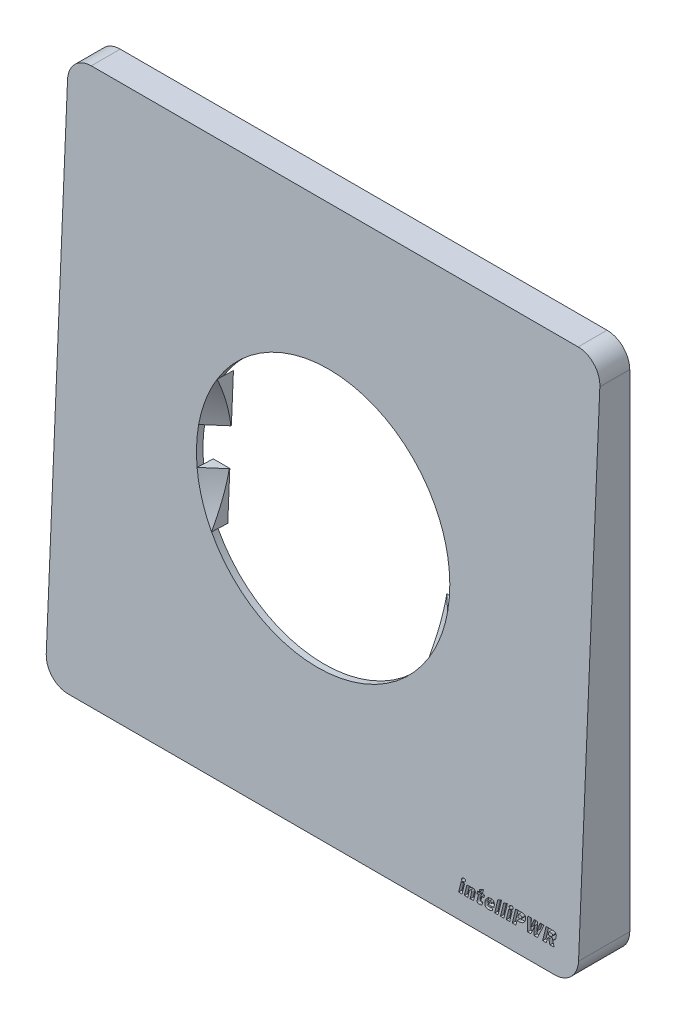
SolidWorks part; units mm, degrees
ref_plane "Front Plane" through (0, 0, 0) normal (0, 0, 1) x (1, 0, 0)
ref_plane "Top Plane" through (0, 0, 0) normal (0, 1, 0) x (1, 0, 0)
ref_plane "Right Plane" through (0, 0, 0) normal (1, 0, 0) x (0, 0, -1)
sketch "Sketch1" plane through (0, 0, 0) normal (0, 0, 1) x (1, 0, 0)
  line L0 (-38.566, 0) -> (72.4153, 0) construction
  line L1 (0, -49.5581) -> (0, 74.5126) construction
  line L2 (-37.5, 40) -> (37.5, 40)
  line L3 (-40, 37.5) -> (-40, -37.5)
  line L4 (-37.5, -40) -> (37.5, -40)
  line L5 (40, 37.5) -> (40, -37.5)
  arc A0 (-40, -37.5) -> (-37.5, -40) centre (-37.5, -37.5) ccw
  arc A1 (37.5, -40) -> (40, -37.5) centre (37.5, -37.5) ccw
  arc A2 (37.5, 40) -> (40, 37.5) centre (37.5, 37.5) cw
  arc A3 (-37.5, 40) -> (-40, 37.5) centre (-37.5, 37.5) ccw
  dimension "D3" = 2.5
  dimension "D1" = 80
  dimension "D2" = 80
  dimension "D4" = 40
  dimension "D5" = 40
extrude "Extrude-Thin1" add sketch "Sketch1" along normal blind 8 thin thin type one direction wall 1
sketch "Sketch5" plane through (41, 0, 0) normal (1, 0, 0) x (0, 0, -1)
  line L0 (20.3178, 0) -> (-25.0092, 0) construction
  line L1 (0, 43.59) -> (0, -45.2443) construction
  line L2 (-3.4562, 41) -> (-8, 41)
  line L3 (-8, 41) -> (-8, -41)
  line L4 (-8, -41) -> (-7.0437, -41)
  line L6 (-7.0437, -41) -> (-3.4562, 41)
  line L7 (-8, -41) -> (0, -41) construction
  line L11 (-8, 41) -> (0, 41) construction
extrude "Cut-Extrude2" cut sketch "Sketch5" against normal blind 120
sketch "Sketch6" plane through (41, 0, 0) normal (1, 0, 0) x (0, 0, -1)
  line L0 (-7.0437, -41) -> (-3.4562, 41)
  line L1 (-3.4562, 41) -> (-4.4572, 41)
  line L2 (-4.4572, 41) -> (-8.0447, -41)
  line L3 (-8.0447, -41) -> (-7.0437, -41)
  line L4 (-3.4562, 41) -> (-3.4562, 45.0301) construction
  dimension "D1" = 1
  dimension "D2" = 90
extrude "Boss-Extrude1" add sketch "Sketch6" against normal blind 82
sketch "Sketch7" plane through (0, 0, 0) normal (0, 0, -1) x (-1, 0, 0)
  line L0 (0, 0) -> (0, 69.537) construction
  line L1 (71.0569, 0) -> (20.5255, 0) construction
  line L2 (-37.5, 41) -> (37.5, 41)
  line L3 (-37.5, 41) -> (37.5, 41) construction
  line L4 (-41, -37.5) -> (-41, 37.5)
  line L5 (41, -37.5) -> (41, 37.5)
  line L6 (-41, -37.5) -> (-41, 37.5) construction
  line L7 (-37.5, -41) -> (37.5, -41)
  arc A0 (37.5, 41) -> (41, 37.5) centre (37.5, 37.5) cw
  arc A1 (-37.5, -41) -> (-41, -37.5) centre (-37.5, -37.5) cw
  arc A2 (37.5, -41) -> (41, -37.5) centre (37.5, -37.5) ccw
  arc A4 (-37.5, 41) -> (-41, 37.5) centre (-37.5, 37.5) ccw
  point P9 (0, -41)
  point P13 (-41, 0)
  point P14 (0, 41)
  point P25 (41, 0)
extrude "Cut-Extrude-Thin1" cut sketch "Sketch7" against normal blind 82 thin thin type one direction wall 11
sketch "Sketch8" plane through (0, 0.273, 6.239) normal (0, 0.0437, 0.999) x (1, 0, 0)
  line L0 (0, 0) -> (0, 28.9526) construction
  line L1 (23.1598, 0) -> (-27.4609, 0) construction
  circle A0 centre (0, 0) radius 19.5
  dimension "D1" = 39
extrude "Cut-Extrude3" cut sketch "Sketch8" against normal blind 82
sketch "Sketch9" plane through (0, 0.273, 6.239) normal (0, 0.0437, 0.999) x (1, 0, 0)
  line L1 (22.5318, -37.8124) -> (22.8563, -36.2774)
  line L3 (22.8563, -36.2774) -> (23.3824, -36.2774)
  line L4 (23.3824, -36.2774) -> (23.058, -37.8124)
  line L5 (23.058, -37.8124) -> (22.5318, -37.8124)
  line L6 (24.2906, -37.8124) -> (24.4746, -36.9301)
  line L7 (24.121, -36.9242) -> (23.9366, -37.8124)
  line L8 (23.9366, -37.8124) -> (23.4104, -37.8124)
  line L9 (23.4104, -37.8124) -> (23.7348, -36.2694)
  line L10 (23.7348, -36.2694) -> (24.261, -36.2694)
  line L11 (24.261, -36.2694) -> (24.2407, -36.3734)
  line L12 (25.0186, -36.8721) -> (24.8197, -37.8124)
  line L13 (24.8197, -37.8124) -> (24.2906, -37.8124)
  line L14 (25.3946, -37.3472) -> (25.5346, -36.6755)
  line L15 (25.5346, -36.6755) -> (25.3007, -36.6755)
  line L16 (25.3007, -36.6755) -> (25.3887, -36.2694)
  line L17 (25.3887, -36.2694) -> (25.6226, -36.2694)
  line L18 (25.6226, -36.2694) -> (25.7042, -35.8811)
  line L19 (25.7042, -35.8811) -> (26.2596, -35.6738)
  line L20 (26.2596, -35.6738) -> (26.134, -36.2694)
  line L21 (26.134, -36.2694) -> (26.4673, -36.2694)
  line L22 (26.4673, -36.2694) -> (26.3797, -36.6755)
  line L23 (26.3797, -36.6755) -> (26.0464, -36.6755)
  line L24 (26.0464, -36.6755) -> (25.9292, -37.2389)
  line L25 (26.2571, -37.3099) -> (26.0929, -37.7574)
  line L26 (27.0891, -36.865) -> (27.5277, -36.865)
  line L27 (27.9194, -37.1898) -> (27.0193, -37.1898)
  line L28 (27.6478, -37.3252) -> (27.7794, -37.6631)
  line L29 (28.0814, -37.8124) -> (28.4875, -35.8849)
  line L30 (28.4875, -35.8849) -> (29.0576, -35.6738)
  line L31 (29.0576, -35.6738) -> (28.6076, -37.8124)
  line L32 (28.6076, -37.8124) -> (28.0814, -37.8124)
  line L33 (28.9747, -37.8124) -> (29.3808, -35.8849)
  line L34 (29.3808, -35.8849) -> (29.951, -35.6738)
  line L35 (29.951, -35.6738) -> (29.5009, -37.8124)
  line L36 (29.5009, -37.8124) -> (28.9747, -37.8124)
  line L37 (29.8681, -37.8124) -> (30.1925, -36.2774)
  line L38 (30.1925, -36.2774) -> (30.7187, -36.2774)
  line L39 (30.7187, -36.2774) -> (30.3943, -37.8124)
  line L40 (30.3943, -37.8124) -> (29.8681, -37.8124)
  line L41 (31.9923, -36.2152) -> (31.6852, -36.2152)
  line L42 (31.6852, -36.2152) -> (31.5858, -36.6755)
  line L43 (31.5858, -36.6755) -> (31.884, -36.6755)
  line L44 (31.7728, -37.1357) -> (31.4894, -37.1357)
  line L45 (31.4894, -37.1357) -> (31.3489, -37.8124)
  line L46 (31.3489, -37.8124) -> (30.7906, -37.8124)
  line L47 (30.7906, -37.8124) -> (31.2233, -35.755)
  line L48 (31.2233, -35.755) -> (32.1031, -35.755)
  line L49 (34.6592, -37.8124) -> (34.1292, -37.8124)
  line L50 (34.1292, -37.8124) -> (34.1292, -37.3658)
  line L51 (33.8492, -37.3658) -> (33.6618, -37.8124)
  line L52 (33.6618, -37.8124) -> (33.1445, -37.8124)
  line L53 (33.1445, -37.8124) -> (33.0891, -35.755)
  line L54 (33.0891, -35.755) -> (33.6737, -35.755)
  line L55 (33.6737, -35.755) -> (33.6563, -36.0989)
  line L56 (33.9309, -36.1019) -> (34.0742, -35.755)
  line L57 (34.0742, -35.755) -> (34.6004, -35.755)
  line L58 (34.6004, -35.755) -> (34.5975, -36.1019)
  line L59 (34.8724, -36.0989) -> (35.001, -35.755)
  line L60 (35.001, -35.755) -> (35.5801, -35.755)
  line L61 (35.5801, -35.755) -> (34.6592, -37.8124)
  line L62 (36.7107, -36.2152) -> (36.3685, -36.2152)
  line L63 (36.3685, -36.2152) -> (36.2721, -36.6755)
  line L64 (36.2721, -36.6755) -> (36.6054, -36.6755)
  line L65 (36.5935, -37.8124) -> (36.4066, -37.1357)
  line L66 (36.4066, -37.1357) -> (36.1786, -37.1357)
  line L67 (36.1786, -37.1357) -> (36.0322, -37.8124)
  line L68 (36.0322, -37.8124) -> (35.4739, -37.8124)
  line L69 (35.4739, -37.8124) -> (35.9066, -35.755)
  line L70 (35.9066, -35.755) -> (36.8215, -35.755)
  line L71 (36.9823, -37.0278) -> (37.228, -37.8124)
  line L72 (37.228, -37.8124) -> (36.5935, -37.8124)
  spline S0 degree 3 poles (23.5051, -35.901) (23.4969, -35.9395) (23.475, -35.9951) (23.4259, -36.0567) (23.38, -36.0941) (23.3281, -36.1243) (23.2494, -36.1531) (23.1859, -36.1615) (23.1426, -36.1611) knots 0 0 0 0 0.243996 0.362518 0.483924 0.60781 0.732572 1 1 1 1
  spline S1 degree 3 poles (23.1426, -36.1611) (23.1034, -36.1614) (23.0464, -36.1543) (22.9794, -36.1247) (22.9459, -36.0992) (22.9246, -36.0749) (22.9109, -36.0553) (22.9015, -36.0333) (22.894, -36.0101) (22.8904, -35.985) (22.8893, -35.9483) (22.8933, -35.92) (22.8973, -35.901) knots 0 0 0 0 0.278361 0.398909 0.514848 0.572098 0.627439 0.683254 0.740687 0.799243 0.862128 1 1 1 1
  spline S2 degree 3 poles (22.8973, -35.901) (22.9046, -35.8648) (22.9269, -35.8129) (22.975, -35.7545) (23.0208, -35.7171) (23.0729, -35.6861) (23.1494, -35.6544) (23.2122, -35.6474) (23.2539, -35.6468) knots 0 0 0 0 0.233169 0.351346 0.477078 0.606225 0.734605 1 1 1 1
  spline S3 degree 3 poles (23.2539, -35.6468) (23.294, -35.6476) (23.3536, -35.6526) (23.4215, -35.6852) (23.4549, -35.7118) (23.4756, -35.7369) (23.4893, -35.7563) (23.4986, -35.7777) (23.5062, -35.8) (23.5103, -35.8237) (23.5118, -35.8577) (23.5094, -35.8837) (23.5051, -35.901) knots 0 0 0 0 0.289932 0.415109 0.533191 0.591068 0.646913 0.702321 0.757398 0.814668 0.873138 1 1 1 1
  spline S4 degree 3 poles (24.4746, -36.9301) (24.4788, -36.907) (24.4857, -36.8741) (24.4892, -36.8319) (24.4898, -36.805) (24.4882, -36.7812) (24.4845, -36.7603) (24.4788, -36.7423) (24.4679, -36.723) (24.4497, -36.7035) (24.4108, -36.6804) (24.3757, -36.6755) (24.3519, -36.6755) knots 0 0 0 0 0.206248 0.294568 0.372668 0.442258 0.50401 0.558886 0.607164 0.698385 0.78958 1 1 1 1
  spline S5 degree 3 poles (24.3519, -36.6755) (24.3255, -36.6748) (24.2865, -36.6813) (24.2396, -36.7028) (24.2139, -36.7214) (24.195, -36.7398) (24.1826, -36.7576) (24.1702, -36.7778) (24.159, -36.8014) (24.1478, -36.8274) (24.1346, -36.8686) (24.1258, -36.9012) (24.121, -36.9242) knots 0 0 0 0 0.211446 0.310999 0.411311 0.464021 0.521401 0.584742 0.653943 0.729878 0.812026 1 1 1 1
  spline S6 degree 3 poles (24.2407, -36.3734) (24.298, -36.3381) (24.3731, -36.2966) (24.4716, -36.2624) (24.5492, -36.2465) (24.6106, -36.2424) (24.6531, -36.2423) knots 0 0 0 0 0.460544 0.581348 0.71025 1 1 1 1
  spline S7 degree 3 poles (24.6531, -36.2423) (24.6921, -36.2424) (24.7488, -36.2462) (24.8195, -36.2639) (24.8654, -36.2813) (24.9061, -36.3046) (24.9414, -36.333) (24.9715, -36.3666) (24.9962, -36.4051) (25.0154, -36.4485) (25.031, -36.4959) (25.0401, -36.5481) (25.0459, -36.6044) (25.0457, -36.6652) (25.0409, -36.7555) (25.0276, -36.8247) (25.0186, -36.8721) knots 0 0 0 0 0.133988 0.193276 0.249258 0.301629 0.353161 0.403793 0.455519 0.509135 0.565969 0.625946 0.690505 0.759591 0.834116 1 1 1 1
  spline S8 degree 3 poles (26.0929, -37.7574) (26.0333, -37.7837) (25.9543, -37.8089) (25.856, -37.8278) (25.7854, -37.8368) (25.7316, -37.8398) (25.6953, -37.8395) knots 0 0 0 0 0.477931 0.605354 0.733676 1 1 1 1
  spline S9 degree 3 poles (25.6953, -37.8395) (25.6631, -37.8397) (25.6164, -37.8366) (25.5579, -37.8244) (25.5198, -37.8123) (25.4862, -37.7963) (25.457, -37.7764) (25.4315, -37.7536) (25.4109, -37.7263) (25.3947, -37.6948) (25.3825, -37.6588) (25.3741, -37.6184) (25.3701, -37.5731) (25.3704, -37.5232) (25.3757, -37.4469) (25.3864, -37.3879) (25.3946, -37.3472) knots 0 0 0 0 0.137072 0.197692 0.25376 0.30627 0.355446 0.403354 0.450795 0.500091 0.55332 0.611471 0.675246 0.745926 0.823384 1 1 1 1
  spline S10 degree 3 poles (25.9292, -37.2389) (25.9236, -37.2632) (25.9182, -37.2972) (25.9231, -37.3387) (25.9338, -37.3601) (25.9509, -37.3746) (25.9818, -37.3894) (26.0096, -37.391) (26.0286, -37.3916) knots 0 0 0 0 0.332431 0.451864 0.549009 0.641836 0.743993 1 1 1 1
  spline S11 degree 3 poles (26.0286, -37.3916) (26.0648, -37.392) (26.1102, -37.3818) (26.1624, -37.3596) (26.204, -37.3401) (26.2353, -37.3223) (26.2571, -37.3099) knots 0 0 0 0 0.439023 0.560347 0.693744 1 1 1 1
  spline S12 degree 3 poles (27.5277, -36.865) (27.5293, -36.8295) (27.529, -36.7789) (27.5142, -36.7178) (27.5009, -36.6876) (27.4872, -36.6673) (27.4736, -36.6552) (27.4583, -36.6443) (27.44, -36.6359) (27.4195, -36.6292) (27.3871, -36.6229) (27.3615, -36.621) (27.3437, -36.6213) knots 0 0 0 0 0.296749 0.416695 0.521302 0.57019 0.620056 0.671542 0.726187 0.786738 0.851475 1 1 1 1
  spline S13 degree 3 poles (27.3437, -36.6213) (27.3155, -36.6212) (27.2732, -36.6284) (27.2232, -36.6548) (27.1894, -36.682) (27.1587, -36.7168) (27.1208, -36.7764) (27.1008, -36.8283) (27.0891, -36.865) knots 0 0 0 0 0.222963 0.331063 0.443598 0.564297 0.695588 1 1 1 1
  spline S14 degree 3 poles (27.946, -37.0879) (27.9408, -37.1068) (27.9333, -37.1411) (27.9259, -37.1755) (27.9194, -37.1898) knots 0 0 0 0 0.556454 1 1 1 1
  spline S15 degree 3 poles (27.0193, -37.1898) (27.0159, -37.2265) (27.016, -37.2792) (27.0367, -37.342) (27.0613, -37.3767) (27.0938, -37.4024) (27.1478, -37.4284) (27.1948, -37.4328) (27.2265, -37.4334) knots 0 0 0 0 0.296056 0.414656 0.524028 0.631631 0.743271 1 1 1 1
  spline S16 degree 3 poles (27.2265, -37.4334) (27.2603, -37.4332) (27.3107, -37.4303) (27.3768, -37.4199) (27.4263, -37.4095) (27.477, -37.3938) (27.5522, -37.3685) (27.6086, -37.3424) (27.6478, -37.3252) knots 0 0 0 0 0.230948 0.344109 0.457558 0.576208 0.706686 1 1 1 1
  spline S17 degree 3 poles (27.7794, -37.6631) (27.7271, -37.6911) (27.6473, -37.7284) (27.5385, -37.7689) (27.4578, -37.7948) (27.3756, -37.8147) (27.2619, -37.8343) (27.1745, -37.8392) (27.1157, -37.8395) knots 0 0 0 0 0.256454 0.380104 0.501569 0.622664 0.745735 1 1 1 1
  spline S18 degree 3 poles (27.1157, -37.8395) (27.0622, -37.8393) (26.9842, -37.8333) (26.8864, -37.8083) (26.822, -37.7829) (26.7641, -37.7507) (26.7129, -37.7122) (26.6679, -37.6684) (26.6299, -37.6183) (26.5991, -37.5624) (26.5744, -37.5016) (26.5568, -37.4353) (26.5454, -37.3642) (26.541, -37.2886) (26.5441, -37.1801) (26.5568, -37.0976) (26.5688, -37.0422) knots 0 0 0 0 0.139839 0.202933 0.262718 0.320042 0.375234 0.429353 0.483442 0.538621 0.595401 0.654489 0.717096 0.783083 0.851913 1 1 1 1
  spline S19 degree 3 poles (26.5688, -37.0422) (26.5831, -36.9792) (26.6085, -36.8876) (26.6551, -36.7729) (26.6947, -36.6953) (26.7382, -36.6235) (26.786, -36.5578) (26.8379, -36.4981) (26.8939, -36.4448) (26.9531, -36.3973) (27.0154, -36.3562) (27.0807, -36.3212) (27.1487, -36.2925) (27.2191, -36.2701) (27.3158, -36.2482) (27.3903, -36.2428) (27.4401, -36.2423) knots 0 0 0 0 0.150666 0.221012 0.288513 0.353593 0.416668 0.477731 0.537737 0.596692 0.654605 0.711686 0.769156 0.826457 0.883737 1 1 1 1
  spline S20 degree 3 poles (27.4401, -36.2423) (27.4892, -36.2427) (27.5612, -36.2476) (27.6515, -36.2705) (27.712, -36.293) (27.7667, -36.323) (27.816, -36.3594) (27.8597, -36.4023) (27.8978, -36.4519) (27.9292, -36.5083) (27.954, -36.5714) (27.9704, -36.6415) (27.9806, -36.718) (27.9827, -36.8011) (27.9759, -36.9259) (27.96, -37.022) (27.946, -37.0879) knots 0 0 0 0 0.125235 0.182282 0.236835 0.289224 0.340575 0.392377 0.44488 0.49922 0.556302 0.616919 0.682128 0.752543 0.828415 1 1 1 1
  spline S21 degree 3 poles (30.8414, -35.901) (30.8332, -35.9395) (30.8113, -35.9951) (30.7621, -36.0567) (30.7163, -36.0941) (30.6643, -36.1243) (30.5857, -36.1531) (30.5221, -36.1615) (30.4789, -36.1611) knots 0 0 0 0 0.243996 0.362518 0.483924 0.60781 0.732572 1 1 1 1
  spline S22 degree 3 poles (30.4789, -36.1611) (30.4396, -36.1614) (30.3826, -36.1543) (30.3156, -36.1247) (30.2822, -36.0992) (30.2609, -36.0749) (30.2472, -36.0553) (30.2378, -36.0333) (30.2303, -36.0101) (30.2266, -35.985) (30.2256, -35.9483) (30.2295, -35.92) (30.2335, -35.901) knots 0 0 0 0 0.278361 0.398909 0.514848 0.572098 0.627439 0.683254 0.740687 0.799243 0.862128 1 1 1 1
  spline S23 degree 3 poles (30.2335, -35.901) (30.2409, -35.8648) (30.2632, -35.8129) (30.3113, -35.7545) (30.3571, -35.7171) (30.4091, -35.6861) (30.4857, -35.6544) (30.5484, -35.6474) (30.5901, -35.6468) knots 0 0 0 0 0.233169 0.351346 0.477078 0.606225 0.734605 1 1 1 1
  spline S24 degree 3 poles (30.5901, -35.6468) (30.6303, -35.6476) (30.6899, -35.6526) (30.7578, -35.6852) (30.7912, -35.7118) (30.8118, -35.7369) (30.8255, -35.7563) (30.8349, -35.7777) (30.8425, -35.8) (30.8465, -35.8237) (30.8481, -35.8577) (30.8456, -35.8837) (30.8414, -35.901) knots 0 0 0 0 0.289932 0.415109 0.533191 0.591068 0.646913 0.702321 0.757398 0.814668 0.873138 1 1 1 1
  spline S25 degree 3 poles (32.1911, -36.4411) (32.1981, -36.411) (32.2031, -36.3661) (32.1907, -36.3103) (32.176, -36.2817) (32.16, -36.2619) (32.1446, -36.2493) (32.1264, -36.2386) (32.1054, -36.2297) (32.081, -36.2237) (32.0434, -36.2164) (32.0132, -36.2152) (31.9923, -36.2152) knots 0 0 0 0 0.254138 0.360693 0.463314 0.514097 0.568127 0.624482 0.687009 0.753851 0.828928 1 1 1 1
  spline S26 degree 3 poles (31.884, -36.6755) (31.9253, -36.6752) (31.9847, -36.6702) (32.0552, -36.6447) (32.0969, -36.6188) (32.1302, -36.5843) (32.1679, -36.5274) (32.184, -36.4765) (32.1911, -36.4411) knots 0 0 0 0 0.29062 0.412092 0.523259 0.631698 0.74585 1 1 1 1
  spline S27 degree 3 poles (32.7583, -36.4322) (32.745, -36.4934) (32.7207, -36.5823) (32.6705, -36.6906) (32.6282, -36.7622) (32.5799, -36.8261) (32.5278, -36.8845) (32.4699, -36.9355) (32.4079, -36.9809) (32.3411, -37.0191) (32.2706, -37.0524) (32.1959, -37.0794) (32.1174, -37.1003) (32.0356, -37.1165) (31.9205, -37.1307) (31.8324, -37.1365) (31.7728, -37.1357) knots 0 0 0 0 0.141358 0.206507 0.268664 0.328624 0.386922 0.444795 0.502156 0.559848 0.618159 0.677698 0.738624 0.801161 0.865596 1 1 1 1
  spline S28 degree 3 poles (32.1031, -35.755) (32.1595, -35.7545) (32.242, -35.7594) (32.3481, -35.7746) (32.4205, -35.7906) (32.4878, -35.8108) (32.5484, -35.8376) (32.6029, -35.8692) (32.6503, -35.9073) (32.6911, -35.9508) (32.7246, -36.0007) (32.7504, -36.057) (32.7685, -36.1196) (32.7791, -36.1885) (32.7814, -36.2941) (32.7698, -36.3761) (32.7583, -36.4322) knots 0 0 0 0 0.148313 0.216935 0.281917 0.343283 0.401251 0.455966 0.508744 0.560452 0.612308 0.666251 0.722712 0.783153 0.849211 1 1 1 1
  spline S29 degree 3 poles (34.1292, -37.3658) (34.1269, -37.284) (34.1283, -37.1605) (34.1355, -36.9976) (34.1408, -36.8793) (34.1467, -36.7691) (34.1519, -36.6833) (34.1555, -36.6211) (34.1605, -36.5706) (34.1642, -36.5352) (34.1677, -36.5134) knots 0 0 0 0 0.287418 0.433707 0.573086 0.703583 0.821712 0.874842 0.922617 1 1 1 1
  spline S30 degree 3 poles (34.1677, -36.5134) (34.1615, -36.5355) (34.1493, -36.5706) (34.134, -36.6213) (34.119, -36.6661) (34.1033, -36.7149) (34.0853, -36.7666) (34.0661, -36.821) (34.0373, -36.8977) (33.9988, -36.9979) (33.9339, -37.161) (33.8835, -37.2843) (33.8492, -37.3658) knots 0 0 0 0 0.075538 0.122272 0.174583 0.231301 0.291254 0.354892 0.421349 0.561229 0.70869 1 1 1 1
  spline S31 degree 3 poles (33.6563, -36.0989) (33.6542, -36.175) (33.6483, -36.2905) (33.6383, -36.4452) (33.6297, -36.5627) (33.6213, -36.6781) (33.6078, -36.821) (33.5985, -36.9253) (33.5916, -36.9923) knots 0 0 0 0 0.254779 0.387257 0.519329 0.649082 0.774717 1 1 1 1
  spline S32 degree 3 poles (33.5916, -36.9923) (33.6117, -36.9251) (33.6463, -36.8211) (33.6993, -36.6803) (33.744, -36.5665) (33.7913, -36.4507) (33.852, -36.2948) (33.8989, -36.1785) (33.9309, -36.1019) knots 0 0 0 0 0.22063 0.344767 0.473491 0.605508 0.738598 1 1 1 1
  spline S33 degree 3 poles (34.5975, -36.1019) (34.5952, -36.1789) (34.5937, -36.2952) (34.5917, -36.4504) (34.5893, -36.5668) (34.5853, -36.6807) (34.577, -36.8224) (34.5688, -36.9258) (34.5624, -36.9923) knots 0 0 0 0 0.259139 0.391547 0.522548 0.65076 0.77529 1 1 1 1
  spline S34 degree 3 poles (34.5624, -36.9923) (34.5824, -36.925) (34.6152, -36.8204) (34.6635, -36.6779) (34.7028, -36.5624) (34.745, -36.445) (34.8026, -36.2905) (34.8461, -36.1755) (34.8724, -36.0989) knots 0 0 0 0 0.222644 0.347664 0.477214 0.609762 0.743344 1 1 1 1
  spline S35 degree 3 poles (36.9121, -36.4407) (36.9178, -36.4114) (36.9227, -36.367) (36.9079, -36.3124) (36.8932, -36.2833) (36.8767, -36.2633) (36.8615, -36.25) (36.8427, -36.2398) (36.822, -36.23) (36.7979, -36.2237) (36.7609, -36.2165) (36.7312, -36.2152) (36.7107, -36.2152) knots 0 0 0 0 0.248425 0.356514 0.461365 0.51411 0.56924 0.626959 0.689289 0.756874 0.831295 1 1 1 1
  spline S36 degree 3 poles (36.6054, -36.6755) (36.6467, -36.6753) (36.706, -36.6701) (36.7764, -36.6438) (36.8177, -36.617) (36.8513, -36.5826) (36.8886, -36.5258) (36.9046, -36.4756) (36.9121, -36.4407) knots 0 0 0 0 0.291424 0.412585 0.525066 0.635143 0.748168 1 1 1 1
  spline S37 degree 3 poles (36.8215, -35.755) (36.8779, -35.7545) (36.9604, -35.7593) (37.0665, -35.7746) (37.139, -35.7905) (37.206, -35.8114) (37.2669, -35.8375) (37.3212, -35.8693) (37.3687, -35.907) (37.41, -35.9497) (37.4431, -35.9994) (37.4698, -36.0545) (37.4882, -36.1161) (37.4992, -36.1841) (37.5021, -36.2884) (37.4911, -36.3696) (37.4793, -36.425) knots 0 0 0 0 0.149106 0.218094 0.283424 0.345229 0.403358 0.458364 0.511193 0.563161 0.614984 0.668363 0.724518 0.784604 0.849908 1 1 1 1
  spline S38 degree 3 poles (37.4793, -36.425) (37.4711, -36.4624) (37.4574, -36.5173) (37.4311, -36.5868) (37.4103, -36.6359) (37.3866, -36.6821) (37.36, -36.7255) (37.3315, -36.7666) (37.2897, -36.8171) (37.2324, -36.8747) (37.1299, -36.9558) (37.0433, -37.0031) (36.9823, -37.0278) knots 0 0 0 0 0.140675 0.207617 0.273118 0.336662 0.398558 0.459984 0.520403 0.639569 0.758048 1 1 1 1
extrude "Cut-Extrude13" cut sketch "Sketch9" against normal blind 0.5
sketch "Çizim2" plane through (0, 0.273, 6.239) normal (0, 0.0437, 0.999) x (1, 0, 0)
  line L0 (0, 29.0101) -> (0, -24.8666) construction
  line L1 (29.1526, 0) -> (-30.9953, 0) construction
  line L2 (19.2979, 2.8) -> (16.75, 2.8)
  line L3 (16.75, 9.9844) -> (16.75, 2.8)
  line L4 (16.75, -9.9844) -> (16.75, -2.8)
  line L5 (-19.2979, 2.8) -> (-16.75, 2.8)
  line L6 (-16.75, 9.9844) -> (-16.75, 2.8)
  line L7 (19.2979, -2.8) -> (16.75, -2.8)
  line L8 (-16.75, -9.9844) -> (-16.75, -2.8)
  line L9 (-19.2979, -2.8) -> (-16.75, -2.8)
  circle A0 centre (0, 0) radius 19.5
  dimension "D2" = 39
  dimension "D1" = 33.5
  dimension "D3" = 5.6
extrude "Yükseklik-Ekstrüzyon1" add sketch "Çizim2" against normal blind 2.5 contours L6 A0 L5 | L9 A0 L8 | L2 A0 L3 | L4 A0 L7
sketch "Çizim3" plane through (0, 0.273, 6.239) normal (0, 0.0437, 0.999) x (1, 0, 0)
  line L0 (0, 0) -> (59.8558, 0) construction
ref_plane "Düzlem1" through (0, 0, 0) normal (0, -0.999, 0.0437) x (-1, 0, 0)
sketch "Çizim4" plane through (0, 0, 0) normal (0, -0.999, 0.0437) x (-1, 0, 0)
  line L0 (0, 22.8886) -> (0, -30.2322) construction
  line L1 (-50.2148, -6.245) -> (60.571, -6.245) construction
  line L3 (19.5, -6.245) -> (16.9, -3.745)
  line L4 (16.9, -3.745) -> (16.9, -6.245)
  line L5 (16.9, -6.245) -> (19.5, -6.245)
  dimension "D1" = 19.5
  dimension "D2" = 2.5
  dimension "D3" = 2.6
revolve "Kes-Döndür2" cut sketch "Çizim4" angle 360 about L0
ref_plane "Düzlem2" through (0, 0, 0) normal (0, 0, -1) x (-1, 0, 0)
sketch "Çizim7" plane through (0, 0, 0) normal (0, 0, -1) x (-1, 0, 0)
  line L0 (0, 0) -> (0, -25.6736) construction
  line L1 (0, 0) -> (31.3225, 0) construction
  line L2 (37.5, -41) -> (-37.5, -41) construction
  line L3 (-41, -37.5) -> (-41, 37.5) construction
  circle A0 centre (-29, -29) radius 5
  circle A1 centre (-29, 29) radius 5
  circle A2 centre (29, 29) radius 5
  circle A3 centre (29, -29) radius 5
  point P21 (0, 0)
  dimension "D3" = 10
  dimension "D1" = 12
  dimension "D2" = 12
  dimension "D4" = 4
extrude "Yükseklik-Ekstrüzyon4" add sketch "Çizim7" against normal up to body
sketch "Çizim8" plane through (0, 0, 0) normal (0, 0, -1) x (-1, 0, 0)
  line L1 (-37.5, 37.5) -> (37.5, 37.5)
  line L2 (-37.5, 37.5) -> (-37.5, -37.5)
  line L3 (-37.5, -37.5) -> (37.5, -37.5)
  line L4 (37.5, 37.5) -> (37.5, -37.5)
extrude "Kes-Ekstrüzyon1" cut sketch "Çizim8" against normal blind 1.5
sketch "Çizim10" plane through (0, -41, 0) normal (0, -1, 0) x (1, 0, 0)
  line L0 (0, 0) -> (0, 11.0435) construction
  line L1 (0, 0) -> (37.9352, 0) construction
  line L5 (16.4791, 4.3882) -> (-16.4791, 4.3882)
  line L6 (-22, 0) -> (22, 0)
  line L7 (-22, 0) -> (-18.6341, 3.4753)
  line L8 (22, 0) -> (18.6341, 3.4753)
  arc A2 (18.6341, 3.4753) -> (16.4791, 4.3882) centre (16.4791, 1.3882) ccw
  arc A3 (-18.6341, 3.4753) -> (-16.4791, 4.3882) centre (-16.4791, 1.3882) cw
  point P20 (0, 0)
  point P21 (0, 4.3882)
extrude "Kes-Ekstrüzyon2" cut sketch "Çizim10" against normal blind 3
sketch "Çizim11" plane through (0, 0, 1.5) normal (0, 0, -1) x (-1, 0, 0)
  circle A0 centre (-29, 29) radius 1.55
  circle A1 centre (29, 29) radius 1.55
  circle A2 centre (29, -29) radius 1.55
  circle A3 centre (-29, -29) radius 1.55
  point P12 (0, 0)
  dimension "D1" = 3.1
  dimension "D2" = 4
extrude "Kes-Ekstrüzyon3" cut sketch "Çizim11" against normal blind 2
